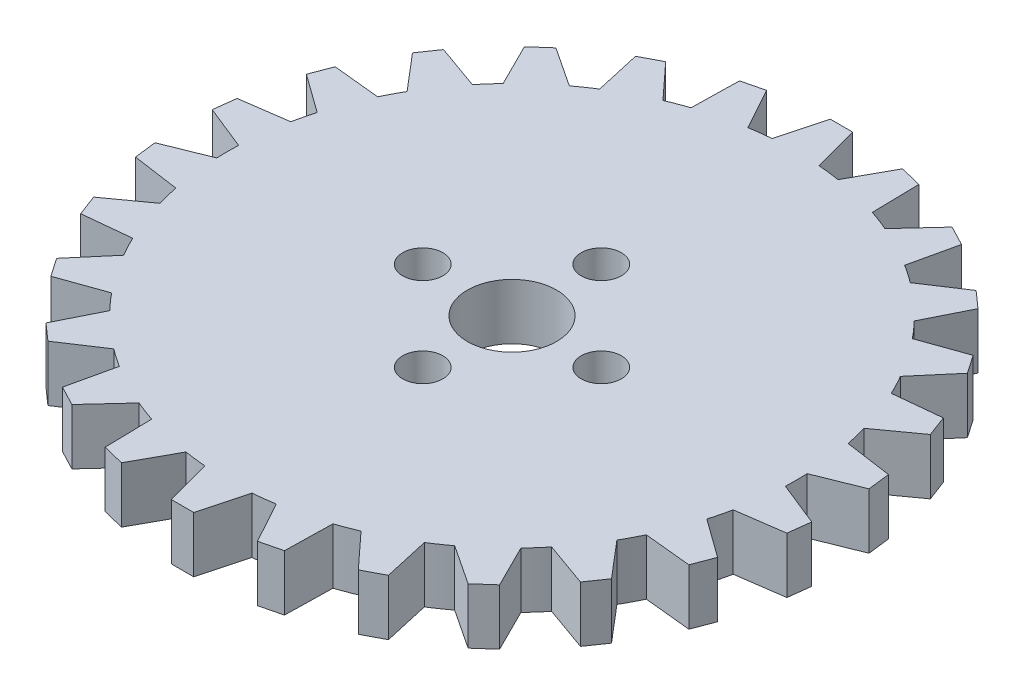
SolidWorks part; units mm, degrees
ref_plane "Front Plane" through (0, 0, 0) normal (0, 0, 1) x (1, 0, 0)
ref_plane "Top Plane" through (0, 0, 0) normal (0, 1, 0) x (1, 0, 0)
ref_plane "Right Plane" through (0, 0, 0) normal (1, 0, 0) x (0, 0, -1)
sketch "Sketch1" plane through (0, 0, 0) normal (0, 1, 0) x (1, 0, 0)
  line L3 (-0.635, 18.7502) -> (0.635, 18.7502)
  line L6 (-0.635, 18.7502) -> (-1.3351, 16.1374)
  line L7 (0.635, 18.7502) -> (1.3351, 16.1374)
  line L8 (5.1038, 18.0534) -> (5.1582, 15.3489)
  line L9 (3.8707, 18.3573) -> (2.5656, 15.988)
  line L10 (3.8707, 18.3573) -> (5.1038, 18.0534)
  line L11 (9.2759, 16.3074) -> (8.6816, 13.6685)
  line L12 (8.1514, 16.8976) -> (6.3172, 14.9094)
  line L13 (8.1514, 16.8976) -> (9.2759, 16.3074)
  line L14 (12.909, 13.6137) -> (11.7004, 11.1936)
  line L15 (11.9584, 14.4558) -> (9.7017, 12.9643)
  line L16 (11.9584, 14.4558) -> (12.909, 13.6137)
  line L17 (15.7918, 10.1287) -> (14.0392, 8.0683)
  line L18 (15.0704, 11.1739) -> (12.5224, 10.2658)
  line L19 (15.0704, 11.1739) -> (15.7918, 10.1287)
  line L20 (17.7569, 6.0552) -> (15.5621, 4.474)
  line L21 (17.3066, 7.2427) -> (14.6153, 6.9707)
  line L22 (17.3066, 7.2427) -> (17.7569, 6.0552)
  line L23 (18.69, 1.6297) -> (16.1806, 0.6198)
  line L24 (18.537, 2.8905) -> (15.8588, 3.2705)
  line L25 (18.537, 2.8905) -> (18.69, 1.6297)
  line L26 (18.537, -2.8905) -> (15.8588, -3.2705)
  line L27 (18.69, -1.6297) -> (16.1806, -0.6198)
  line L28 (18.69, -1.6297) -> (18.537, -2.8905)
  line L29 (17.3066, -7.2427) -> (14.6153, -6.9707)
  line L30 (17.7569, -6.0552) -> (15.5621, -4.474)
  line L31 (17.7569, -6.0552) -> (17.3066, -7.2427)
  line L32 (15.0704, -11.1739) -> (12.5224, -10.2658)
  line L33 (15.7918, -10.1287) -> (14.0392, -8.0683)
  line L34 (15.7918, -10.1287) -> (15.0704, -11.1739)
  line L35 (11.9584, -14.4558) -> (9.7017, -12.9643)
  line L36 (12.909, -13.6137) -> (11.7004, -11.1936)
  line L37 (12.909, -13.6137) -> (11.9584, -14.4558)
  line L38 (8.1514, -16.8976) -> (6.3172, -14.9094)
  line L39 (9.2759, -16.3074) -> (8.6816, -13.6685)
  line L40 (9.2759, -16.3074) -> (8.1514, -16.8976)
  line L41 (3.8707, -18.3573) -> (2.5656, -15.988)
  line L42 (5.1038, -18.0534) -> (5.1582, -15.3489)
  line L43 (5.1038, -18.0534) -> (3.8707, -18.3573)
  line L44 (-0.635, -18.7502) -> (-1.3351, -16.1374)
  line L45 (0.635, -18.7502) -> (1.3351, -16.1374)
  line L46 (0.635, -18.7502) -> (-0.635, -18.7502)
  line L47 (-5.1038, -18.0534) -> (-5.1582, -15.3489)
  line L48 (-3.8707, -18.3573) -> (-2.5656, -15.988)
  line L49 (-3.8707, -18.3573) -> (-5.1038, -18.0534)
  line L50 (-9.2759, -16.3074) -> (-8.6816, -13.6685)
  line L51 (-8.1514, -16.8976) -> (-6.3172, -14.9094)
  line L52 (-8.1514, -16.8976) -> (-9.2759, -16.3074)
  line L53 (-12.909, -13.6137) -> (-11.7004, -11.1936)
  line L54 (-11.9584, -14.4558) -> (-9.7017, -12.9643)
  line L55 (-11.9584, -14.4558) -> (-12.909, -13.6137)
  line L56 (-15.7918, -10.1287) -> (-14.0392, -8.0683)
  line L57 (-15.0704, -11.1739) -> (-12.5224, -10.2658)
  line L58 (-15.0704, -11.1739) -> (-15.7918, -10.1287)
  line L59 (-17.7569, -6.0552) -> (-15.5621, -4.474)
  line L60 (-17.3066, -7.2427) -> (-14.6153, -6.9707)
  line L61 (-17.3066, -7.2427) -> (-17.7569, -6.0552)
  line L62 (-18.69, -1.6297) -> (-16.1806, -0.6198)
  line L63 (-18.537, -2.8905) -> (-15.8588, -3.2705)
  line L64 (-18.537, -2.8905) -> (-18.69, -1.6297)
  line L65 (-18.537, 2.8905) -> (-15.8588, 3.2705)
  line L66 (-18.69, 1.6297) -> (-16.1806, 0.6198)
  line L67 (-18.69, 1.6297) -> (-18.537, 2.8905)
  line L68 (-17.3066, 7.2427) -> (-14.6153, 6.9707)
  line L69 (-17.7569, 6.0552) -> (-15.5621, 4.474)
  line L70 (-17.7569, 6.0552) -> (-17.3066, 7.2427)
  line L71 (-15.0704, 11.1739) -> (-12.5224, 10.2658)
  line L72 (-15.7918, 10.1287) -> (-14.0392, 8.0683)
  line L73 (-15.7918, 10.1287) -> (-15.0704, 11.1739)
  line L74 (-11.9584, 14.4558) -> (-9.7017, 12.9643)
  line L75 (-12.909, 13.6137) -> (-11.7004, 11.1936)
  line L76 (-12.909, 13.6137) -> (-11.9584, 14.4558)
  line L77 (-8.1514, 16.8976) -> (-6.3172, 14.9094)
  line L78 (-9.2759, 16.3074) -> (-8.6816, 13.6685)
  line L79 (-9.2759, 16.3074) -> (-8.1514, 16.8976)
  line L80 (-3.8707, 18.3573) -> (-2.5656, 15.988)
  line L81 (-5.1038, 18.0534) -> (-5.1582, 15.3489)
  line L82 (-5.1038, 18.0534) -> (-3.8707, 18.3573)
  circle A0 centre (0, 0) radius 16.1925
  arc A1 (-0.1397, 16.1919) -> (1.0795, 16.1565) centre (0, 0) cw
  arc A2 (-1.3351, 16.1374) -> (1.3351, 16.1374) centre (0, 0) cw
  arc A3 (2.5656, 15.988) -> (5.1582, 15.3489) centre (0, 0) cw
  arc A4 (6.3172, 14.9094) -> (8.6816, 13.6685) centre (0, 0) cw
  arc A5 (9.7017, 12.9643) -> (11.7004, 11.1936) centre (0, 0) cw
  arc A6 (12.5224, 10.2658) -> (14.0392, 8.0683) centre (0, 0) cw
  arc A7 (14.6153, 6.9707) -> (15.5621, 4.474) centre (0, 0) cw
  arc A8 (15.8588, 3.2705) -> (16.1806, 0.6198) centre (0, 0) cw
  arc A9 (16.1806, -0.6198) -> (15.8588, -3.2705) centre (0, 0) cw
  arc A10 (15.5621, -4.474) -> (14.6153, -6.9707) centre (0, 0) cw
  arc A11 (14.0392, -8.0683) -> (12.5224, -10.2658) centre (0, 0) cw
  arc A12 (11.7004, -11.1936) -> (9.7017, -12.9643) centre (0, 0) cw
  arc A13 (8.6816, -13.6685) -> (6.3172, -14.9094) centre (0, 0) cw
  arc A14 (5.1582, -15.3489) -> (2.5656, -15.988) centre (0, 0) cw
  arc A15 (1.3351, -16.1374) -> (-1.3351, -16.1374) centre (0, 0) cw
  arc A16 (-2.5656, -15.988) -> (-5.1582, -15.3489) centre (0, 0) cw
  arc A17 (-6.3172, -14.9094) -> (-8.6816, -13.6685) centre (0, 0) cw
  arc A18 (-9.7017, -12.9643) -> (-11.7004, -11.1936) centre (0, 0) cw
  arc A19 (-12.5224, -10.2658) -> (-14.0392, -8.0683) centre (0, 0) cw
  arc A20 (-14.6153, -6.9707) -> (-15.5621, -4.474) centre (0, 0) cw
  arc A21 (-15.8588, -3.2705) -> (-16.1806, -0.6198) centre (0, 0) cw
  arc A22 (-16.1806, 0.6198) -> (-15.8588, 3.2705) centre (0, 0) cw
  arc A23 (-15.5621, 4.474) -> (-14.6153, 6.9707) centre (0, 0) cw
  arc A24 (-14.0392, 8.0683) -> (-12.5224, 10.2658) centre (0, 0) cw
  arc A25 (-11.7004, 11.1936) -> (-9.7017, 12.9643) centre (0, 0) cw
  arc A26 (-8.6816, 13.6685) -> (-6.3172, 14.9094) centre (0, 0) cw
  arc A27 (-5.1582, 15.3489) -> (-2.5656, 15.988) centre (0, 0) cw
  point P9 (0, 18.7502)
  dimension "D3" = 32.385
  dimension "D1" = 1.27
  dimension "D2" = 2.6128
  dimension "D4" = 105
  dimension "D5" = 75
  dimension "D8" = 26
extrude "Boss-Extrude1" add sketch "Sketch1" along normal blind 3.175
sketch "Sketch2" plane through (0, 0, 0) normal (0, 1, 0) x (1, 0, 0)
  circle A1 centre (-5.08, 0) radius 1.143
  circle A2 centre (0, 5.08) radius 1.143
  circle A3 centre (5.08, 0) radius 1.143
  circle A4 centre (0, -5.08) radius 1.143
  circle A5 centre (0, 0) radius 2.54
  dimension "D1" = 2.286
  dimension "D2" = 2.286
  dimension "D3" = 2.286
  dimension "D4" = 2.286
  dimension "D9" = 5.08
  dimension "D5" = 5.08
  dimension "D6" = 5.08
  dimension "D7" = 5.08
  dimension "D8" = 5.08
extrude "Cut-Extrude1" cut sketch "Sketch2" along normal blind 3.175
